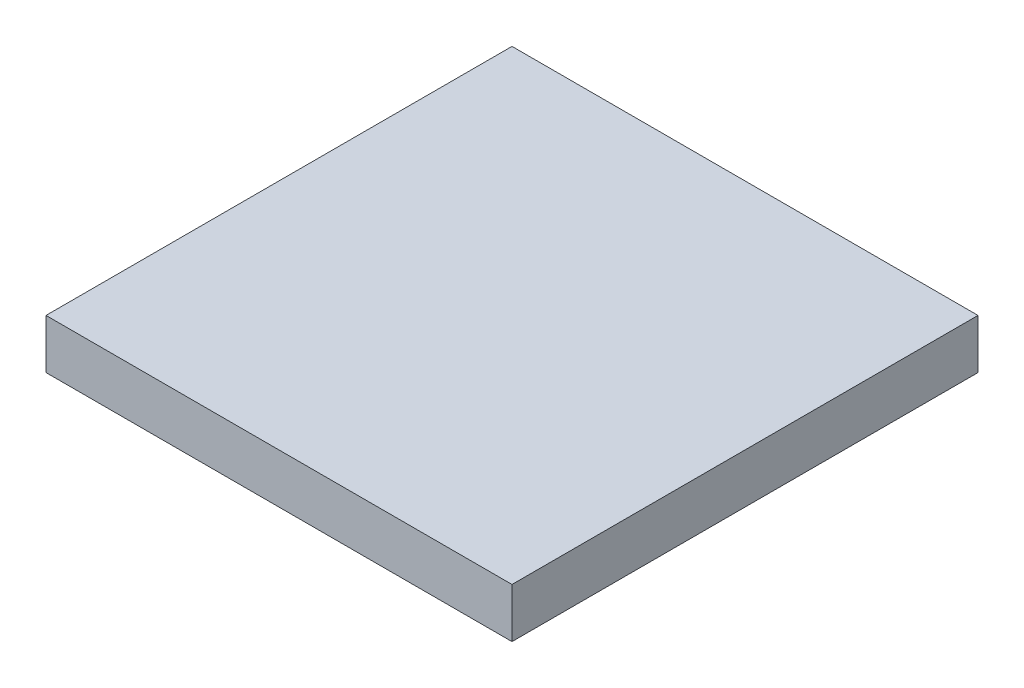
SolidWorks part; units mm, degrees
ref_plane "Front Plane" through (0, 0, 0) normal (0, 0, 1) x (1, 0, 0)
ref_plane "Top Plane" through (0, 0, 0) normal (0, 1, 0) x (1, 0, 0)
ref_plane "Right Plane" through (0, 0, 0) normal (1, 0, 0) x (0, 0, -1)
sketch "Sketch1" plane through (0, 0, 0) normal (0, 1, 0) x (1, 0, 0)
  line L1 (0, 0) -> (8, 0)
  line L2 (0, 0) -> (0, 8)
  line L3 (0, 8) -> (8, 8)
  line L4 (8, 0) -> (8, 8)
  dimension "D1" = 8
  dimension "D2" = 8
extrude "Boss-Extrude1" add sketch "Sketch1" along normal blind 0.85
